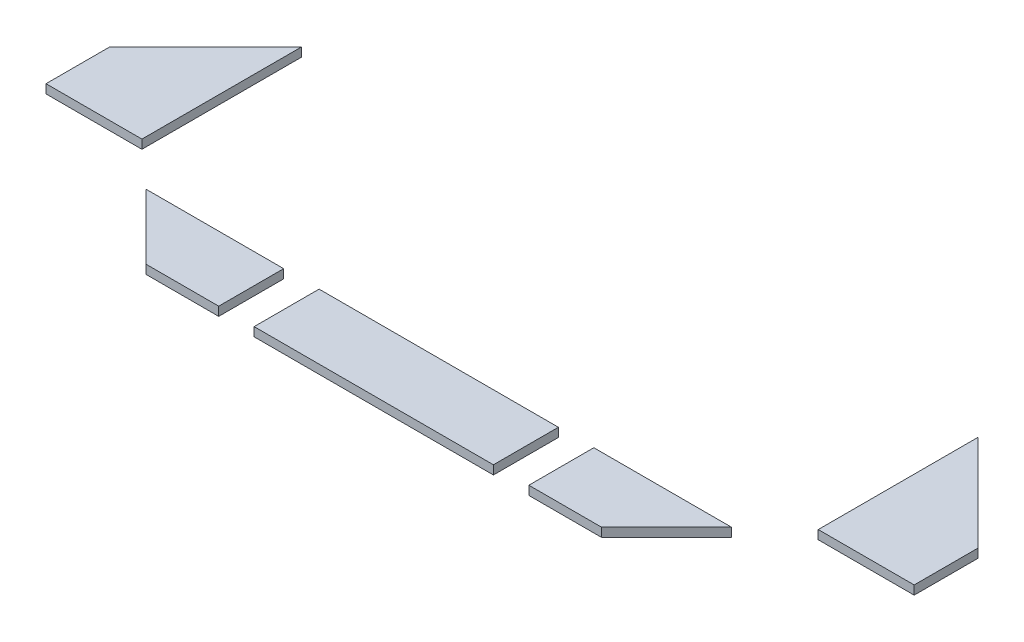
SolidWorks part; units mm, degrees
ref_plane "Front Plane" through (0, 0, 0) normal (0, 0, 1) x (1, 0, 0)
ref_plane "Top Plane" through (0, 0, 0) normal (0, 1, 0) x (1, 0, 0)
ref_plane "Right Plane" through (0, 0, 0) normal (1, 0, 0) x (0, 0, -1)
sketch "Sketch1" plane through (0, 0, 0) normal (0, 1, 0) x (1, 0, 0)
  line L0 (-36.5, 18.5) -> (-36.5, 45.5)
  line L1 (0, 0) -> (41.5147, 0) construction
  line L2 (0, 0) -> (0, 12) construction
  line L3 (0, 12) -> (41.5147, 12) construction
  line L4 (41.5147, 0) -> (41.5147, 12) construction
  line L6 (41.0147, 0.5) -> (41.0147, 11.5)
  line L7 (0.5, 11.5) -> (41.0147, 11.5)
  line L8 (0.5, 0.5) -> (0.5, 11.5)
  line L9 (0.5, 0.5) -> (41.0147, 0.5)
  line L10 (41.5147, 0) -> (41.5147, 12) construction
  line L11 (-18, 0) -> (-30, 12) construction
  line L12 (-30, 12) -> (-5, 12) construction
  line L13 (-5, 12) -> (-5, 0) construction
  line L14 (-5, 0) -> (-18, 0) construction
  line L15 (-17.7929, 0.5) -> (-28.7929, 11.5)
  line L16 (-28.7929, 11.5) -> (-5.5, 11.5)
  line L17 (-5.5, 11.5) -> (-5.5, 0.5)
  line L18 (-5.5, 0.5) -> (-17.7929, 0.5)
  line L19 (-36, 18) -> (-36, 46) construction
  line L20 (-36, 46) -> (-36.7574, 46) construction
  line L21 (-36.7574, 46) -> (-53.2426, 29.5147) construction
  line L22 (-53.2426, 29.5147) -> (-53.2426, 18) construction
  line L23 (-53.2426, 18) -> (-36, 18) construction
  line L28 (20.7574, 0.5) -> (20.7574, 11.5) construction
  line L34 (47.0147, 0.5) -> (59.3076, 0.5)
  line L35 (47.0147, 11.5) -> (47.0147, 0.5)
  line L36 (70.3076, 11.5) -> (47.0147, 11.5)
  line L37 (59.3076, 0.5) -> (70.3076, 11.5)
  line L42 (-36.5, 45.5) -> (-36.5503, 45.5)
  line L43 (-36.5503, 45.5) -> (-52.7426, 29.3076)
  line L44 (-52.7426, 29.3076) -> (-52.7426, 18.5)
  line L45 (-52.7426, 18.5) -> (-36.5, 18.5)
  line L46 (94.2574, 18.5) -> (78.0147, 18.5)
  line L47 (94.2574, 29.3076) -> (94.2574, 18.5)
  line L48 (78.065, 45.5) -> (94.2574, 29.3076)
  line L49 (78.0147, 45.5) -> (78.065, 45.5)
  line L50 (78.0147, 18.5) -> (78.0147, 45.5)
  point P17 (-36.5, 18.5)
  point P28 (-36.5, 46.5)
  point P35 (0, 0)
  dimension "D1" = 0.5
  dimension "D2" = 12
  dimension "D3" = 0.5
  dimension "D4" = 0.5
extrude "Boss-Extrude1" add sketch "Sketch1" along normal blind 1.5
